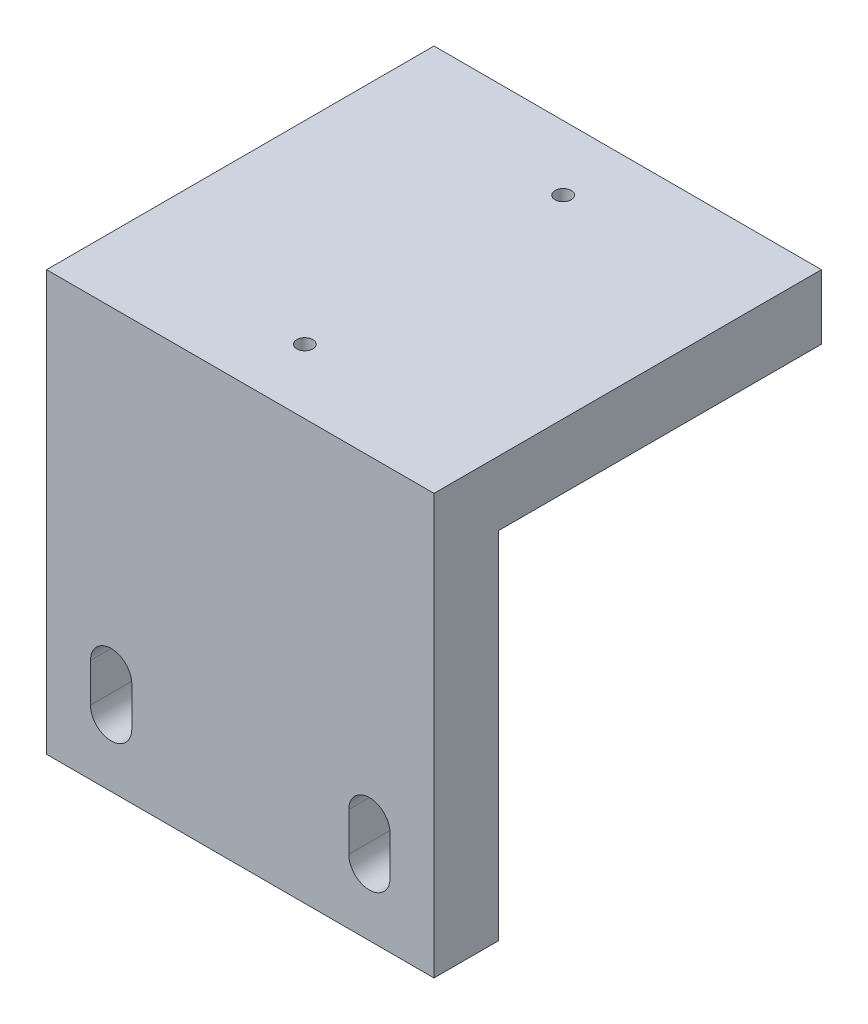
SolidWorks part; units mm, degrees
ref_plane "前视基准面" through (0, 0, 0) normal (0, 0, 1) x (1, 0, 0)
ref_plane "上视基准面" through (0, 0, 0) normal (0, 1, 0) x (1, 0, 0)
ref_plane "右视基准面" through (0, 0, 0) normal (1, 0, 0) x (0, 0, -1)
sketch "草图1" plane through (0, 0, 0) normal (0, 0, 1) x (1, 0, 0)
  line L1 (30, -32.5) -> (-30, -32.5)
  line L2 (30, -32.5) -> (30, 32.5)
  line L3 (30, 32.5) -> (-30, 32.5)
  line L4 (-30, -32.5) -> (-30, 32.5)
  line L5 (30, -32.5) -> (-30, 32.5) construction
  line L6 (30, 32.5) -> (-30, -32.5) construction
  point P0 (0, 0)
  dimension "D1" = 65
  dimension "D2" = 60
extrude "凸台-拉伸1" add sketch "草图1" along normal blind 60
sketch "草图2" plane through (0, 0, 0) normal (0, 0, -1) x (-1, 0, 0)
  line L0 (30, 32.5) -> (30, -32.5) construction
  line L1 (-30, -32.5) -> (30, -32.5)
  line L2 (-30, -32.5) -> (-30, 22.5)
  line L3 (-30, 22.5) -> (30, 22.5)
  line L4 (30, -32.5) -> (30, 22.5)
  line L5 (-30, 32.5) -> (30, 32.5) construction
  dimension "D1" = 10
extrude "切除-拉伸1" cut sketch "草图2" against normal offset from surface (50 mm away) 10 up to face at (0, 0, 60)
sketch "草图3" plane through (0, 0, 60) normal (0, 0, 1) x (1, 0, 0)
  line L0 (-20, -22.5) -> (-20, -16.5) construction
  line L1 (-23.2, -22.5) -> (-23.2, -16.5)
  line L2 (-16.8, -22.5) -> (-16.8, -16.5)
  line L3 (0, -32.5) -> (0, -19.5) construction
  line L4 (-30, -32.5) -> (30, -32.5) construction
  line L5 (0, -19.5) -> (-20, -19.5) construction
  line L6 (20, -22.5) -> (20, -16.5) construction
  line L7 (23.2, -22.5) -> (23.2, -16.5)
  line L8 (16.8, -22.5) -> (16.8, -16.5)
  arc A0 (-23.2, -22.5) -> (-16.8, -22.5) centre (-20, -22.5) ccw
  arc A1 (-16.8, -16.5) -> (-23.2, -16.5) centre (-20, -16.5) ccw
  arc A2 (23.2, -22.5) -> (16.8, -22.5) centre (20, -22.5) cw
  arc A3 (16.8, -16.5) -> (23.2, -16.5) centre (20, -16.5) cw
  point P2 (-20, -19.5)
  point P15 (20, -19.5)
  dimension "D2" = 3.2
  dimension "D1" = 40
  dimension "D3" = 6
  dimension "D4" = 10
extrude "切除-拉伸2" cut sketch "草图3" against normal through all
sketch "草图4" plane through (0, 32.5, 0) normal (0, 1, 0) x (1, 0, 0)
  line L0 (0, 0) -> (0, -50) construction
  line L1 (30, 0) -> (-30, 0) construction
  circle A0 centre (0, -50) radius 3.6086
  circle A1 centre (0, -10) radius 2.5092
  dimension "D1" = 40
  dimension "D2" = 10
hole_wizard "M3 螺纹孔1" positions "3D草图1" profile "草图5" tap size "M3" standard "Iso"
sketch3d "3D草图1"
  point P0 (0, 32.5, 10)
  point P3 (0, 32.5, 50)
sketch "草图5" plane through (0, 32.5, 10) normal (1, 0, 0) x (0, 0, 1)
  line L0 (0, 0) -> (0, 8.2511)
  line L1 (0, 8.2511) -> (1.25, 7.5)
  line L2 (1.25, 7.5) -> (1.25, 0)
  line L5 (1.25, 0) -> (0, 0)
  line L10 (0, 8.2511) -> (-1.25, 7.5) construction
  line L11 (0, -6.35) -> (0, 107.95) construction
  dimension "螺纹孔钻头直径" = 2.5
  dimension "螺纹孔钻头深度" = 7.5
  dimension "导头角度" = 118
